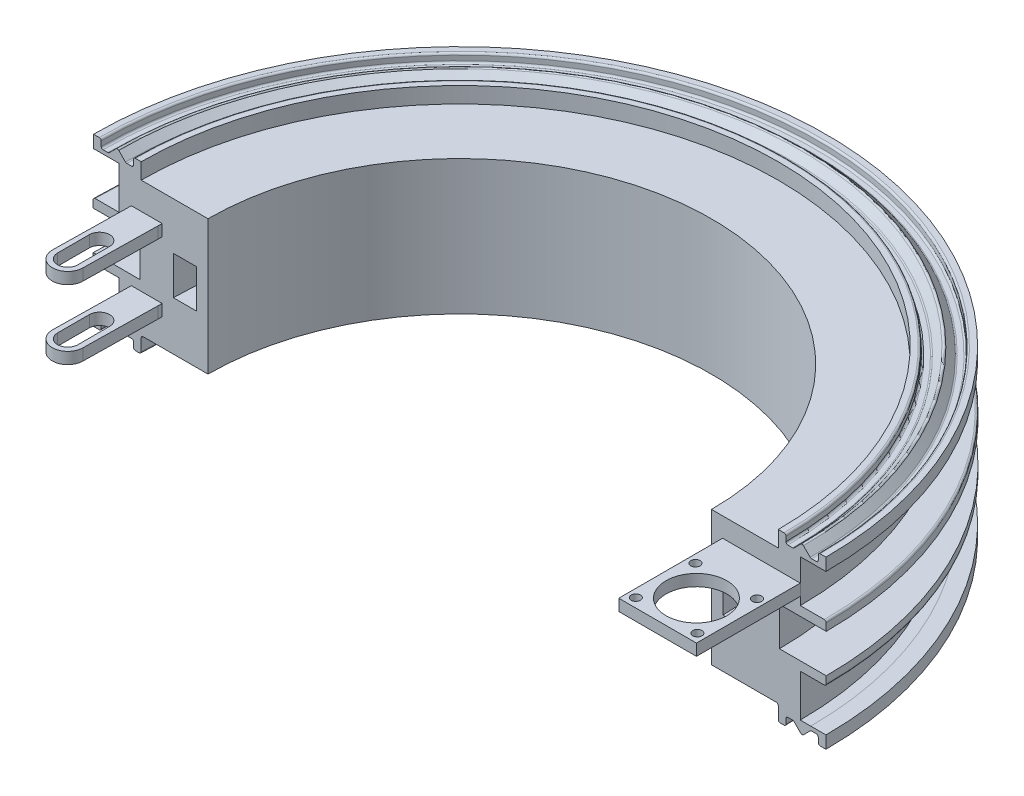
SolidWorks part; units mm, degrees
ref_plane "Front Plane" through (0, 0, 0) normal (0, 0, 1) x (1, 0, 0)
ref_plane "Top Plane" through (0, 0, 0) normal (0, 1, 0) x (1, 0, 0)
ref_plane "Right Plane" through (0, 0, 0) normal (1, 0, 0) x (0, 0, -1)
sketch "Sketch1" plane through (0, 0, 0) normal (0, 0, 1) x (1, 0, 0)
  line L0 (0, 21.2431) -> (0, -20.7935) construction
  line L1 (0, 21.2431) -> (0, -13.7569)
  line L12 (-17.6709, -1.3005) -> (-17.6709, 8.6995)
  line L14 (-29.847, 8.6995) -> (-29.847, 11.1239)
  line L23 (0, 3.7431) -> (-36.1577, 3.7431) construction
  line L25 (-9, 8.9508) -> (-3, 8.9508)
  line L26 (-9, 8.9508) -> (-9, -1.0492)
  line L27 (-9, -1.0492) -> (-3, -1.0492)
  line L28 (-3, 8.9508) -> (-3, -1.0492)
  line L29 (-21.3184, 23.1426) -> (-23.5684, 25.3926)
  line L30 (-23.5684, 25.3926) -> (-25.8184, 23.1426)
  line L32 (-25.8184, 22.1426) -> (-23.0909, 22.1426)
  line L33 (-23.0909, 22.1426) -> (-23.0909, 11.1239)
  line L34 (-23.0909, 11.1239) -> (-29.847, 11.1239)
  line L35 (-29.847, -3.6377) -> (-23.0909, -3.6377)
  line L42 (-29.847, -3.6377) -> (-29.847, -1.3005)
  line L43 (-29.847, -1.3005) -> (-17.6709, -1.3005)
  line L44 (-29.847, 8.6995) -> (-17.6709, 8.6995)
  line L45 (-21.3184, 23.1426) -> (-19.3684, 23.1426)
  line L46 (-19.3684, 23.1426) -> (-19.3684, 25.4025)
  line L47 (-17.3684, 25.4025) -> (-17.3684, 21.2431)
  line L48 (-17.3684, 21.2431) -> (0, 21.2431)
  line L49 (-19.3684, 25.4025) -> (-17.3684, 25.4025)
  line L50 (-25.8184, 23.1426) -> (-27.7684, 23.1426)
  line L51 (-27.7684, 23.1426) -> (-27.7684, 25.3862)
  line L52 (-27.7684, 25.3862) -> (-29.7684, 25.3862)
  line L53 (-29.7684, 25.3862) -> (-29.7684, 22.1426)
  line L54 (-29.7684, 22.1426) -> (-25.8184, 22.1426)
  line L65 (-29.7684, -14.6564) -> (-25.8184, -14.6564)
  line L66 (-29.7684, -17.9) -> (-29.7684, -14.6564)
  line L67 (-27.7684, -17.9) -> (-29.7684, -17.9)
  line L68 (-27.7684, -15.6564) -> (-27.7684, -17.9)
  line L69 (-25.8184, -15.6564) -> (-27.7684, -15.6564)
  line L70 (-19.3684, -17.9163) -> (-17.3684, -17.9163)
  line L71 (-17.3684, -13.7569) -> (0, -13.7569)
  line L72 (-17.3684, -17.9163) -> (-17.3684, -13.7569)
  line L73 (-19.3684, -15.6564) -> (-19.3684, -17.9163)
  line L74 (-21.3184, -15.6564) -> (-19.3684, -15.6564)
  line L75 (-23.0909, -14.6564) -> (-23.0909, -3.6377)
  line L76 (-25.8184, -14.6564) -> (-23.0909, -14.6564)
  line L77 (-23.5684, -17.9064) -> (-25.8184, -15.6564)
  line L78 (-21.3184, -15.6564) -> (-23.5684, -17.9064)
  line L79 (-29.847, 8.6995) -> (-29.847, -5.9646) construction
  line L80 (-23.5684, 25.3926) -> (-40.3715, 25.3926) construction
  line L81 (-40.3715, 25.3926) -> (-10.8825, 25.3926) construction
  line L82 (-23.0909, 11.1239) -> (-23.0909, -3.6377) construction
  dimension "D1" = 35
  dimension "D2" = 1.95
  dimension "D3" = 1
  dimension "D4" = 4.5
  dimension "D5" = 3
  dimension "D6" = 2
  dimension "D7" = 2
  dimension "D8" = 10
  dimension "D9" = 5.4201
  dimension "D10" = 10
  dimension "D11" = 6
sketch "Sketch3" plane through (0, 0, 0) normal (0, 1, 0) x (1, 0, 0)
  arc A0 (0, 0) -> (130.92, 0) centre (65.46, 0) cw
sweep "Sweep3" add profiles "Sketch1" path "Sketch3"
sketch "Sketch13" plane through (0, 0, 0) normal (0, 0, 1) x (1, 0, 0)
  line L4 (-9, 3.9508) -> (-9, 18.9333) construction
  line L5 (-9, -1.0492) -> (-9, 8.9508) construction
  line L6 (-9, 18.9333) -> (-9, -5.0069) construction
  line L7 (-17.6709, 3.6995) -> (-1.1121, 3.6995) construction
  line L8 (-17.6709, 8.6995) -> (-17.6709, -1.3005) construction
  line L9 (-16.2449, 7.1426) -> (-16.2449, 2.1426) construction
  line L15 (-19.9387, -3.8005) -> (-11.9387, -3.8005)
  line L16 (-11.9387, -3.8005) -> (-11.9387, -6.8005)
  line L22 (-11.9387, -6.8005) -> (-19.9387, -6.8005)
  line L23 (-19.9387, -6.8005) -> (-19.9387, -3.8005)
  line L24 (-19.9387, 11.1995) -> (-11.9387, 11.1995)
  line L25 (-19.9387, 14.1995) -> (-19.9387, 11.1995)
  line L26 (-11.9387, 14.1995) -> (-19.9387, 14.1995)
  line L27 (-11.9387, 11.1995) -> (-11.9387, 14.1995)
  dimension "D1" = 3
  dimension "D2" = 8
  dimension "D3" = 7.5
ref_plane "Plane3" through (0, 3.6995, 0) normal (0, 1, 0) x (1, 0, 0)
sketch "Sketch17" plane through (0, 0, 0) normal (0, 0, 1) x (1, 0, 0)
  line L15 (154.0109, 16.1931) -> (133.8109, 16.1931)
  line L16 (154.0109, 22.1426) -> (154.0109, 11.1239) construction
  line L17 (133.8109, 16.1931) -> (133.8109, 13.1931)
  line L18 (133.8109, 13.1931) -> (154.0109, 13.1931)
  line L19 (154.0109, 13.1931) -> (154.0109, 16.1931)
  line L20 (130.92, 21.2431) -> (148.2883, 21.2431) construction
  dimension "D1" = 5.05
  dimension "D2" = 3
  dimension "D3" = 20.2
fillet "Fillet1" radius 0.5 1 edges at (65.46, 25.3926, -89.0284)
fillet "Fillet2" radius 0.5 1 edges at (65.46, 23.1426, -91.2784)
fillet "Fillet3" radius 0.5 1 edges at (65.46, 23.1426, -93.2284)
fillet "Fillet4" radius 0.5 2 edges at (65.46, 23.1426, -84.8284) (65.46, 23.1426, -86.7784)
fillet "Fillet5" radius 0.5 3 edges at (65.46, -17.9163, -84.8284) (65.46, -15.6564, -86.7784) (65.46, -17.9064, -89.0284)
fillet "Fillet6" radius 0.5 3 edges at (65.46, -13.7569, -82.8284) (65.46, -17.9163, -82.8284) (65.46, -15.6564, -84.8284)
fillet "Fillet7" radius 0.5 3 edges at (65.46, -15.6564, -91.2784) (65.46, -17.9, -93.2284) (65.46, -15.6564, -93.2284)
fillet "Fillet9" radius 0.5 2 edges at (65.46, -3.6377, -95.3069) (65.46, 11.1239, -95.3069)
fillet "Fillet10" radius 0.5 2 edges at (65.46, 25.3862, -93.2284) (65.46, 25.4025, -84.8284)
extrude "Boss-Extrude6" add sketch "Sketch13" along normal blind 1
sketch "Sketch19" plane through (0, 14.1995, 0) normal (0, 1, 0) x (1, 0, 0)
  line L0 (-19.9387, -1) -> (-20.2411, -20.2365)
  line L1 (-11.9387, -1) -> (-12.2411, -20.2365)
  line L2 (-18.8911, -20.2365) -> (-18.8911, -11.973)
  line L3 (-13.5911, -20.2365) -> (-13.5911, -11.973)
  circle A0 centre (-16.2411, -20.2365) radius 2.65
  circle A1 centre (-16.2411, -20.2365) radius 4
  circle A2 centre (-16.2411, -11.973) radius 2.65
  line M5 (-19.9387, -1) -> (-11.9387, -1)
  dimension "D1" = 5.3
  dimension "D2" = 7.999
extrude "Boss-Extrude7" add sketch "Sketch19" against normal blind 3 contours A1 L1 L0 M5 | L1 A1 A0
mirror "Mirror1" about plane through (0, 3.6995, 0) normal (0, 1, 0) of "Boss-Extrude6", "Boss-Extrude7"
extrude "Boss-Extrude8" add sketch "Sketch17" along normal blind 27 contours L15 L17 L18 L19
sketch "Sketch21" plane through (0, 13.1931, 0) normal (0, -1, 0) x (1, 0, 0)
  line L0 (133.8109, 27) -> (154.0109, 27) construction
  line L1 (133.8109, 27) -> (133.8109, 0) construction
  line L3 (143.9109, 16.9) -> (130.587, 16.9) construction
  line L4 (130.587, 16.9) -> (159.1422, 16.9) construction
  line L5 (143.9109, 16.9) -> (143.9109, 26.1323) construction
  line L6 (143.9109, 26.1323) -> (143.9109, -1.5088) construction
  circle A0 centre (143.9109, 16.9) radius 7.9
  circle A1 centre (135.9085, 24.65) radius 1.2
  circle A2 centre (135.9085, 9.15) radius 1.2
  circle A3 centre (151.9132, 9.15) radius 1.2
  circle A4 centre (151.9132, 24.65) radius 1.2
  dimension "D1" = 10.1
  dimension "D3" = 11.14
  dimension "D2" = 10.1
  dimension "D4" = 2.35
extrude "Cut-Extrude3" cut sketch "Sketch21" against normal blind 22.2
